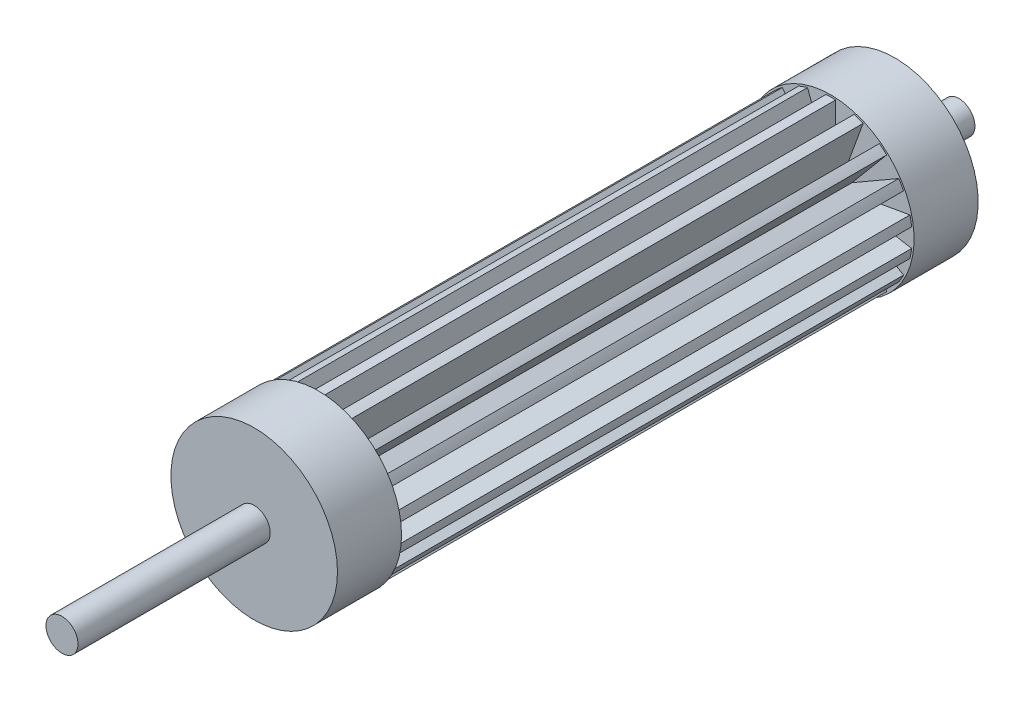
SolidWorks part; units mm, degrees
ref_plane "Front Plane" through (0, 0, 0) normal (0, 0, 1) x (1, 0, 0)
ref_plane "Top Plane" through (0, 0, 0) normal (0, 1, 0) x (1, 0, 0)
ref_plane "Right Plane" through (0, 0, 0) normal (1, 0, 0) x (0, 0, -1)
sketch "Sketch1" plane through (0, 0, 0) normal (0, 0, 1) x (1, 0, 0)
  circle A0 centre (0, 0) radius 6.35
  dimension "D1" = 12.7
extrude "Boss-Extrude1" add sketch "Sketch1" along normal blind 300
sketch "Sketch2" plane through (0, 0, 300) normal (0, 0, 1) x (1, 0, 0)
  line L1 (-1.5, -50.8) -> (1.5, -50.8)
  line L2 (-1.5, -50.8) -> (-1.5, 50.8)
  line L3 (-1.5, 50.8) -> (1.5, 50.8)
  line L4 (1.5, -50.8) -> (1.5, 50.8)
  line L5 (-1.5, -50.8) -> (1.5, 50.8) construction
  line L6 (-1.5, 50.8) -> (1.5, -50.8) construction
  point P0 (0, 0)
  dimension "D1" = 3
  dimension "D2" = 101.6
extrude "Boss-Extrude2" add sketch "Sketch2" against normal through all
pattern_circular "CirPattern1" count 9 over 360 about axis through (0, 0, 0) along (0, 0, 1) of "Boss-Extrude2"
sketch "Sketch9" plane through (0, 0, 300) normal (0, 0, 1) x (1, 0, 0)
  circle A0 centre (0, 0) radius 25.4
  circle A1 centre (0, 0) radius 60.0249
  dimension "D1" = 50.8
extrude "Cut-Extrude1" cut sketch "Sketch9" against normal blind 317.2
sketch "Sketch11" plane through (0, 0, 0) normal (0, 1, 0) x (1, 0, 0)
  line L10 (-106.5721, -200) -> (103.3813, -200)
  line L11 (-106.5721, -200) -> (-106.5721, -600)
  line L12 (-106.5721, -600) -> (103.3813, -600)
  line L13 (103.3813, -200) -> (103.3813, -600)
  dimension "D1" = 200
  dimension "D2" = 400
extrude "Cut-Extrude2" cut sketch "Sketch11" against normal mid plane 317.2
sketch "Sketch13" plane through (0, 0, 0) normal (0, 0, 1) x (1, 0, 0)
  circle A0 centre (0, 0) radius 5
  dimension "D1" = 10
extrude "Boss-Extrude3" add sketch "Sketch13" along normal blind 260 and the other way blind 20
sketch "Sketch14" plane through (0, 0, 0) normal (0, 0, -1) x (-1, 0, 0)
  circle A0 centre (0, 0) radius 26
  dimension "D1" = 52
extrude "Boss-Extrude4" add sketch "Sketch14" against normal blind 20
sketch "Sketch15" plane through (0, 0, 200) normal (0, 0, 1) x (1, 0, 0)
  circle A0 centre (0, 0) radius 26
  dimension "D1" = 52
extrude "Boss-Extrude5" add sketch "Sketch15" against normal blind 20
